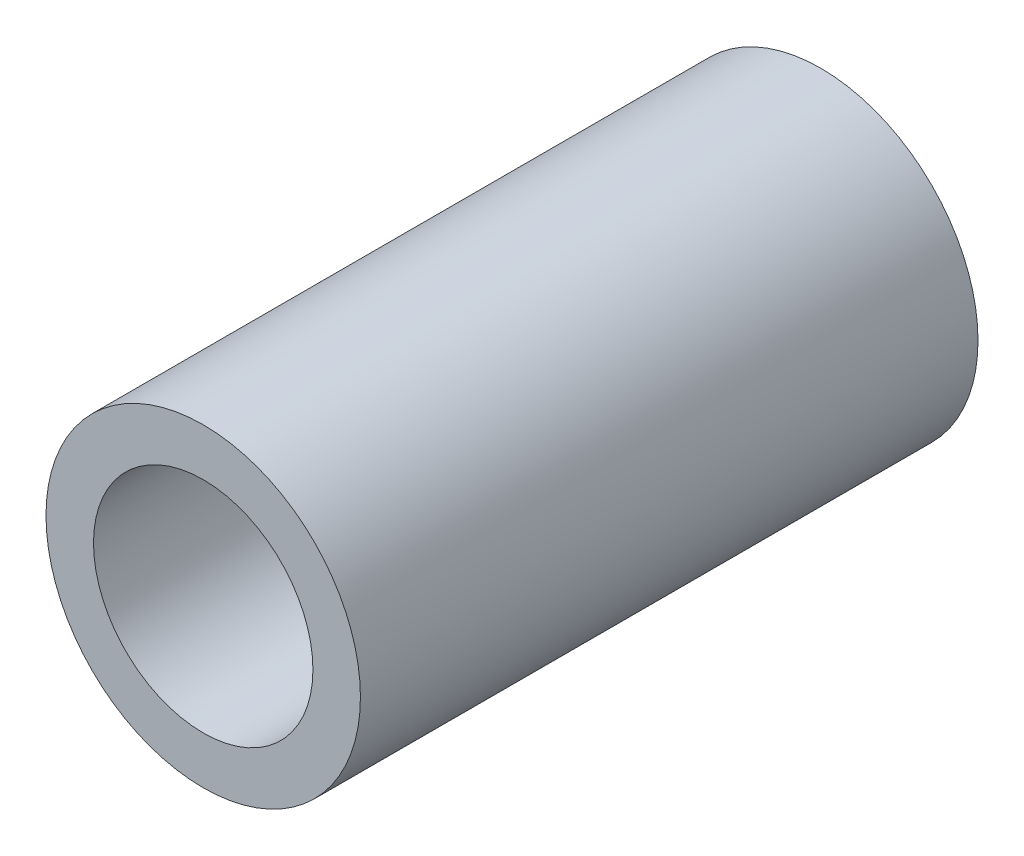
SolidWorks part; units mm, degrees
ref_plane "Front" through (0, 0, 0) normal (0, 0, 1) x (1, 0, 0)
ref_plane "Top" through (0, 0, 0) normal (0, 1, 0) x (1, 0, 0)
ref_plane "Right" through (0, 0, 0) normal (1, 0, 0) x (0, 0, -1)
sketch "Sketch1" plane through (0, 0, 0) normal (0, 0, 1) x (1, 0, 0)
  line L1 (7.3323, 0) -> (3.6662, 6.35)
  line L2 (3.6662, 6.35) -> (-3.6662, 6.35)
  line L3 (-3.6662, 6.35) -> (-7.3323, 0)
  line L4 (-7.3323, 0) -> (-3.6662, -6.35)
  line L5 (-3.6662, -6.35) -> (3.6662, -6.35)
  line L6 (3.6662, -6.35) -> (7.3323, 0)
  circle A0 centre (0, 0) radius 6.35 construction
  circle A1 centre (0, 0) radius 10.5073
  circle A2 centre (0, 0) radius 7.3323
  dimension "D1" = 3.175
  dimension "D2" = 12.7
extrude "Boss-Extrude1" add sketch "Sketch1" along normal blind 41.275 contours A1 A2
